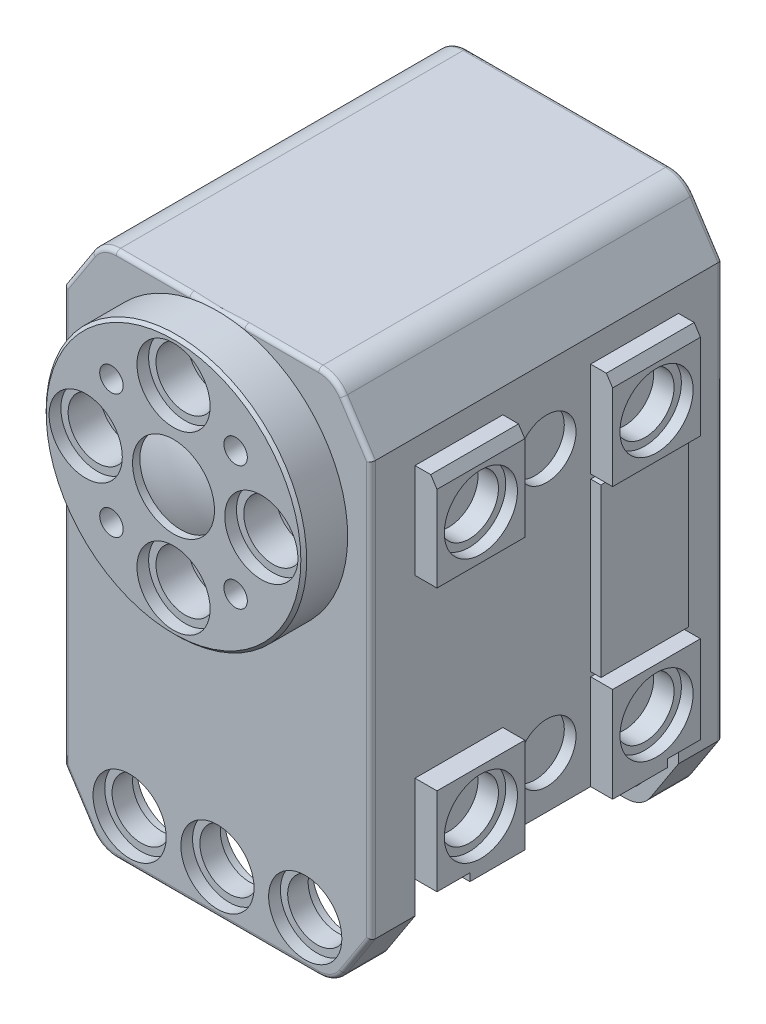
SolidWorks part; units mm, degrees
ref_plane "Front Plane" through (0, 0, 0) normal (0, 0, 1) x (1, 0, 0)
ref_plane "Top Plane" through (0, 0, 0) normal (0, 1, 0) x (1, 0, 0)
ref_plane "Right Plane" through (0, 0, 0) normal (1, 0, 0) x (0, 0, -1)
sketch "Sketch1" plane through (0, 0, 0) normal (0, 1, 0) x (1, 0, 0)
  line L0 (8.9, -12) -> (0, -12)
  line L1 (0, -12) -> (0, -15)
  line L2 (2.8, -14.5) -> (2.8, -15)
  line L3 (2.8, -15) -> (8.9, -15)
  line L4 (8.9, -15) -> (8.9, -12)
  line L5 (0, -12) -> (0, -15) construction
  arc A0 (0, -15) -> (2.8, -14.5) centre (0, -6.91) ccw
revolve "Revolve1" add sketch "Sketch1" angle 360 about L5
ref_plane "Plane1" through (0, 0, 12) normal (0, 0, 1) x (1, 0, 0)
sketch "Sketch2" plane through (0, 0, 12) normal (0, 0, 1) x (1, 0, 0)
  line L0 (12, -23.1503) -> (12, 5.1503)
  line L1 (12, 5.1503) -> (10.5, 5.1503)
  line L2 (10.5, 5.1503) -> (8, 9)
  line L3 (8, 9) -> (-8, 9)
  line L4 (-8, 9) -> (-10.5, 5.1503)
  line L5 (-10.5, 5.1503) -> (-12, 5.1503)
  line L6 (-12, 5.1503) -> (-12, -21.5)
  line L7 (-12, -21.5) -> (-11.5717, -21.5)
  line L8 (-11.5717, -21.5) -> (-8, -27)
  line L9 (-8, -27) -> (8, -27)
  line L10 (8, -27) -> (10.5, -23.1503)
  line L11 (10.5, -23.1503) -> (12, -23.1503)
extrude "Boss-Extrude1" add sketch "Sketch2" against normal blind 3
sketch "Sketch3" plane through (0, -23.1503, 0) normal (0, -1, 0) x (1, 0, 0)
  line L0 (10.5, 9) -> (12, 9)
  line L1 (12, 9) -> (12, 12)
  line L2 (12, 12) -> (10.5, 12)
  line L3 (10.5, 12) -> (10.5, 9)
extrude "Cut-Extrude1" cut sketch "Sketch3" against normal blind 1.6503
sketch "Sketch4" plane through (0, 0, 9) normal (0, 0, -1) x (-1, 0, 0)
  line L0 (-10.5, 5.1503) -> (-8, 9)
  line L1 (-8, 9) -> (8, 9)
  line L2 (8, 9) -> (10.5, 5.1503)
  line L3 (10.5, 5.1503) -> (12, 5.1503)
  line L4 (12, 5.1503) -> (12, -21.5)
  line L5 (12, -21.5) -> (6, -21.5)
  line L6 (4, -22.5) -> (-4, -22.5)
  line L7 (-6, -21.5) -> (-12, -21.5)
  line L8 (-12, -21.5) -> (-12, 5.1503)
  line L9 (-12, 5.1503) -> (-10.5, 5.1503)
  arc A0 (6, -21.5) -> (4, -22.5) centre (6, -24) ccw
  arc A1 (-4, -22.5) -> (-6, -21.5) centre (-6, -24) ccw
extrude "Boss-Extrude2" add sketch "Sketch4" along normal blind 18
sketch "Sketch5" plane through (0, 0, 12) normal (0, 0, 1) x (1, 0, 0)
  line L0 (12, -21.5) -> (12, 5.1503)
  line L1 (12, 5.1503) -> (10.5, 5.1503)
  line L2 (10.5, 5.1503) -> (10.5, -21.5)
  line L3 (10.5, -21.5) -> (12, -21.5)
extrude "Cut-Extrude2" cut sketch "Sketch5" against normal blind 3
sketch "Sketch6" plane through (0, 0, 9) normal (0, 0, -1) x (-1, 0, 0)
  line L0 (10.5, -21.5) -> (10.5, -23.1503)
  line L1 (10.5, -23.1503) -> (11.5717, -21.5)
  line L2 (11.5717, -21.5) -> (10.5, -21.5)
extrude "Cut-Extrude3" cut sketch "Sketch6" against normal through all
sketch "Sketch7" plane through (0, 0, 12) normal (0, 0, 1) x (1, 0, 0)
  line L0 (-10.5, -21.5) -> (-10.5, 5.1503)
  line L1 (-10.5, 5.1503) -> (-12, 5.1503)
  line L2 (-12, 5.1503) -> (-12, -21.5)
  line L3 (-12, -21.5) -> (-10.5, -21.5)
extrude "Cut-Extrude4" cut sketch "Sketch7" against normal blind 3
sketch "Sketch8" plane through (0, 5.1503, 0) normal (0, 1, 0) x (-1, 0, 0)
  line L0 (-12, 9) -> (-12, -9)
  line L1 (-12, -9) -> (-10.5, -9)
  line L2 (-10.5, -9) -> (-10.5, 9)
  line L3 (-10.5, 9) -> (-12, 9)
extrude "Cut-Extrude5" cut sketch "Sketch8" against normal blind 20.1503
sketch "Sketch9" plane through (0, 0, -9) normal (0, 0, -1) x (-1, 0, 0)
  line L0 (-12, -15) -> (-12, -21.5)
  line L1 (-12, -21.5) -> (-10.5, -21.5)
  line L2 (-10.5, -21.5) -> (-10.5, -15)
  line L3 (-10.5, -15) -> (-12, -15)
extrude "Cut-Extrude6" cut sketch "Sketch9" against normal blind 12
sketch "Sketch10" plane through (0, 0, -9) normal (0, 0, -1) x (-1, 0, 0)
  line L0 (-10.5, -20.975) -> (-10.5, -21.5)
  line L1 (-10.5, -21.5) -> (-6, -21.5)
  line L2 (-4, -22.5) -> (-3.3731, -22.5)
  line L3 (-6, -20.975) -> (-10.5, -20.975)
  arc A0 (-6, -21.5) -> (-4, -22.5) centre (-6, -24) cw
  arc A1 (-3.3731, -22.5) -> (-6, -20.975) centre (-6, -24) ccw
extrude "Cut-Extrude7" cut sketch "Sketch10" against normal blind 2.25
sketch "Sketch11" plane through (0, 0, -9) normal (0, 0, -1) x (-1, 0, 0)
  line L0 (3.3731, -22.5) -> (4, -22.5)
  line L1 (6, -21.5) -> (12, -21.5)
  line L2 (12, -21.5) -> (12, -20.975)
  line L3 (12, -20.975) -> (6, -20.975)
  arc A0 (6, -20.975) -> (3.3731, -22.5) centre (6, -24) ccw
  arc A1 (4, -22.5) -> (6, -21.5) centre (6, -24) cw
extrude "Cut-Extrude8" cut sketch "Sketch11" against normal blind 2.25
sketch "Sketch12" plane through (0, 0, 9) normal (0, 0, 1) x (1, 0, 0)
  line L0 (3.3731, -22.5) -> (4, -22.5)
  line L1 (6, -21.5) -> (12, -21.5)
  line L2 (12, -21.5) -> (12, -20.975)
  line L3 (12, -20.975) -> (6, -20.975)
  arc A0 (6, -20.975) -> (3.3731, -22.5) centre (6, -24) ccw
  arc A1 (4, -22.5) -> (6, -21.5) centre (6, -24) cw
extrude "Cut-Extrude9" cut sketch "Sketch12" against normal blind 2.25
sketch "Sketch13" plane through (0, 0, 9) normal (0, 0, 1) x (1, 0, 0)
  line L0 (-6, -20.975) -> (-12, -20.975)
  line L1 (-12, -20.975) -> (-12, -21.5)
  line L2 (-12, -21.5) -> (-6, -21.5)
  line L3 (-4, -22.5) -> (-3.3731, -22.5)
  arc A0 (-3.3731, -22.5) -> (-6, -20.975) centre (-6, -24) ccw
  arc A1 (-6, -21.5) -> (-4, -22.5) centre (-6, -24) cw
extrude "Cut-Extrude10" cut sketch "Sketch13" against normal blind 2.25
sketch "Sketch14" plane through (0, 5.1503, 0) normal (0, 1, 0) x (-1, 0, 0)
  line L0 (10.5, 9) -> (10.5, -3)
  line L1 (10.5, -3) -> (12, -3)
  line L2 (12, -3) -> (12, 9)
  line L3 (12, 9) -> (10.5, 9)
extrude "Cut-Extrude11" cut sketch "Sketch14" against normal blind 20.1503
ref_plane "Plane2" through (0, 0, -3) normal (0, 0, -1) x (-1, 0, 0)
sketch "Sketch15" plane through (0, 0, -3) normal (0, 0, -1) x (-1, 0, 0)
  line L0 (10.5, -15) -> (10.5, -21.5)
  line L1 (10.5, -21.5) -> (12, -21.5)
  line L2 (12, -21.5) -> (12, -15)
  line L3 (12, -15) -> (10.5, -15)
extrude "Cut-Extrude12" cut sketch "Sketch15" against normal blind 6
sketch "Sketch16" plane through (0, 5.1503, 0) normal (0, 1, 0) x (-1, 0, 0)
  line L0 (12, -3) -> (10.5, -3)
  line L1 (10.5, -3) -> (10.5, -9)
  line L2 (10.5, -9) -> (12, -9)
  line L3 (12, -9) -> (12, -3)
extrude "Cut-Extrude13" cut sketch "Sketch16" against normal blind 20.1503
sketch "Sketch17" plane through (10.5, 0, 0) normal (1, 0, 0) x (0, 0, -1)
  line L0 (3, -21.5) -> (3, -15)
  line L1 (3, -15) -> (9, -15)
  line L2 (9, -15) -> (9, -20.975)
  line L3 (9, -20.975) -> (6.75, -20.975)
  line L4 (6.75, -20.975) -> (6.75, -21.5)
  line L5 (6.75, -21.5) -> (3, -21.5)
extrude "Boss-Extrude3" add sketch "Sketch17" along normal blind 1.5
sketch "Sketch18" plane through (0, 0, -9) normal (0, 0, -1) x (-1, 0, 0)
  line L0 (-8, 9) -> (8, 9)
  line L1 (8, 9) -> (10.5, 5.1503)
  line L2 (10.5, 5.1503) -> (10.5, -23.1503)
  line L3 (10.5, -23.1503) -> (8, -27)
  line L4 (8, -27) -> (-8, -27)
  line L5 (-8, -27) -> (-10.5, -23.1503)
  line L6 (-10.5, -23.1503) -> (-10.5, 5.1503)
  line L7 (-10.5, 5.1503) -> (-8, 9)
extrude "Boss-Extrude4" add sketch "Sketch18" along normal blind 3
sketch "Sketch19" plane through (0, 0, 9) normal (0, 0, -1) x (-1, 0, 0)
  circle A0 centre (6, -24) radius 2.5
extrude "Cut-Extrude14" cut sketch "Sketch19" against normal blind 0.8
sketch "Sketch20" plane through (0, 0, 12) normal (0, 0, 1) x (1, 0, 0)
  circle A0 centre (-6, -24) radius 2.5
extrude "Cut-Extrude15" cut sketch "Sketch20" against normal blind 0.8
sketch "Sketch21" plane through (0, 0, 11.2) normal (0, 0, 1) x (1, 0, 0)
  circle A0 centre (-6, -24) radius 2
extrude "Cut-Extrude16" cut sketch "Sketch21" against normal up to next
sketch "Sketch22" plane through (0, 0, -9) normal (0, 0, 1) x (1, 0, 0)
  circle A0 centre (-6, -24) radius 2.5
extrude "Cut-Extrude17" cut sketch "Sketch22" against normal blind 0.8
sketch "Sketch23" plane through (0, 0, -12) normal (0, 0, -1) x (-1, 0, 0)
  circle A0 centre (6, -24) radius 2.5
extrude "Cut-Extrude18" cut sketch "Sketch23" against normal blind 0.8
sketch "Sketch24" plane through (0, 0, -11.2) normal (0, 0, -1) x (-1, 0, 0)
  circle A0 centre (6, -24) radius 2
extrude "Cut-Extrude19" cut sketch "Sketch24" against normal up to next
sketch "Sketch25" plane through (-10.5, 0, 0) normal (-1, 0, 0) x (0, 0, 1)
  line L0 (3, 3.5) -> (9, 3.5)
  line L1 (9, 3.5) -> (9, -3)
  line L2 (9, -3) -> (3, -3)
  line L3 (3, -3) -> (3, 3.5)
extrude "Boss-Extrude5" add sketch "Sketch25" along normal blind 1.5
sketch "Sketch26" plane through (-10.5, 0, 0) normal (-1, 0, 0) x (0, 0, 1)
  line L0 (-3, -3) -> (-9, -3)
  line L1 (-9, -3) -> (-9, 3.5)
  line L2 (-9, 3.5) -> (-3, 3.5)
  line L3 (-3, 3.5) -> (-3, -3)
extrude "Boss-Extrude6" add sketch "Sketch26" along normal blind 1.5
sketch "Sketch27" plane through (10.5, 0, 0) normal (1, 0, 0) x (0, 0, -1)
  line L0 (-3, -3) -> (-9, -3)
  line L1 (-9, -3) -> (-9, 3.5)
  line L2 (-9, 3.5) -> (-3, 3.5)
  line L3 (-3, 3.5) -> (-3, -3)
extrude "Boss-Extrude7" add sketch "Sketch27" along normal blind 1.5
sketch "Sketch28" plane through (10.5, 0, 0) normal (1, 0, 0) x (0, 0, -1)
  line L0 (3, 3.5) -> (9, 3.5)
  line L1 (9, 3.5) -> (9, -3)
  line L2 (9, -3) -> (3, -3)
  line L3 (3, -3) -> (3, 3.5)
extrude "Boss-Extrude8" add sketch "Sketch28" along normal blind 1.5
sketch "Sketch29" plane through (10.5, 0, 0) normal (1, 0, 0) x (0, 0, -1)
  line L0 (3, -3.3) -> (9, -3.3)
  line L1 (9, -3.3) -> (9, -14.7)
  line L2 (9, -14.7) -> (3, -14.7)
  line L3 (3, -14.7) -> (3, -3.3)
extrude "Boss-Extrude9" add sketch "Sketch29" along normal blind 0.7
sketch "Sketch30" plane through (-10.5, 0, 0) normal (-1, 0, 0) x (0, 0, 1)
  line L0 (-3, -14.7) -> (-9, -14.7)
  line L1 (-9, -14.7) -> (-9, -3.3)
  line L2 (-9, -3.3) -> (-3, -3.3)
  line L3 (-3, -3.3) -> (-3, -14.7)
extrude "Boss-Extrude10" add sketch "Sketch30" along normal blind 0.7
ref_plane "Plane3" through (0, -24, 0) normal (0, 1, 0) x (1, 0, 0)
sketch "Sketch31" plane through (0, -24, 0) normal (0, 1, 0) x (1, 0, 0)
  line L0 (2.5, -9) -> (0, -9)
  line L1 (0, -9) -> (0, -12)
  line L2 (0, -12) -> (2.5, -12)
  line L3 (2.5, -12) -> (2.5, -11.2)
  line L4 (2.5, -11.2) -> (2, -11.2)
  line L5 (2, -11.2) -> (2, -9.8)
  line L6 (2, -9.8) -> (2.5, -9.8)
  line L7 (2.5, -9.8) -> (2.5, -9)
  line L8 (0, -9) -> (0, -12) construction
revolve "Cut-Revolve1" cut sketch "Sketch31" angle 360 about L8
sketch "Sketch32" plane through (0, -24, 0) normal (0, 1, 0) x (1, 0, 0)
  line L0 (2.5, 12) -> (0, 12)
  line L1 (0, 12) -> (0, 9)
  line L2 (0, 9) -> (2.5, 9)
  line L3 (2.5, 9) -> (2.5, 9.8)
  line L4 (2.5, 9.8) -> (2, 9.8)
  line L5 (2, 9.8) -> (2, 11.2)
  line L6 (2, 11.2) -> (2.5, 11.2)
  line L7 (2.5, 11.2) -> (2.5, 12)
  line L8 (0, 12) -> (0, 9) construction
revolve "Cut-Revolve2" cut sketch "Sketch32" angle 360 about L8
sketch "Sketch33" plane through (0, -24, 0) normal (0, 1, 0) x (1, 0, 0)
  line L0 (8.5, 12) -> (6, 12)
  line L1 (6, 12) -> (6, 9)
  line L2 (6, 9) -> (8.5, 9)
  line L3 (8.5, 9) -> (8.5, 9.8)
  line L4 (8.5, 9.8) -> (8, 9.8)
  line L5 (8, 9.8) -> (8, 11.2)
  line L6 (8, 11.2) -> (8.5, 11.2)
  line L7 (8.5, 11.2) -> (8.5, 12)
  line L8 (6, 12) -> (6, 9) construction
revolve "Cut-Revolve3" cut sketch "Sketch33" angle 360 about L8
sketch "Sketch34" plane through (0, -24, 0) normal (0, 1, 0) x (1, 0, 0)
  line L0 (8.5, -9) -> (6, -9)
  line L1 (6, -9) -> (6, -12)
  line L2 (6, -12) -> (8.5, -12)
  line L3 (8.5, -12) -> (8.5, -11.2)
  line L4 (8.5, -11.2) -> (8, -11.2)
  line L5 (8, -11.2) -> (8, -9.8)
  line L6 (8, -9.8) -> (8.5, -9.8)
  line L7 (8.5, -9.8) -> (8.5, -9)
  line L8 (6, -9) -> (6, -12) construction
revolve "Cut-Revolve4" cut sketch "Sketch34" angle 360 about L8
hole_wizard "Ø4.0 (4) Diameter Hole1" positions "Sketch36" profile "Sketch35" hole size "Ø4.0" standard "ANSI Metric"
sketch "Sketch36" plane through (-10.5, 0, 0) normal (-1, 0, 0) x (0, 0, 1)
  point P0 (0, 0)
  point P1 (0, -18)
sketch "Sketch35" plane through (-10.5, 0, 0) normal (0, 1, 0) x (0, 0, 1)
  line L0 (0, 0) -> (0, 0.8)
  line L1 (0, 0.8) -> (2, 0.8)
  line L2 (2, 0.8) -> (2, 0)
  line L5 (2, 0) -> (0, 0)
  line L10 (0, 0.8) -> (-2, 0.8) construction
  line L11 (0, -6.35) -> (0, 107.95) construction
  dimension "Hole Dia." = 4
  dimension "Hole Depth" = 0.8
  dimension "Drill Angle" = 180
hole_wizard "Ø4.0 (4) Diameter Hole2" positions "Sketch38" profile "Sketch37" hole size "Ø4.0" standard "ANSI Metric"
sketch "Sketch38" plane through (10.5, 0, 0) normal (1, 0, 0) x (0, 0, -1)
  point P0 (0, 0)
  point P1 (0, -18)
sketch "Sketch37" plane through (10.5, 0, 0) normal (0, 1, 0) x (0, 0, -1)
  line L0 (0, 0) -> (0, 0.8)
  line L1 (0, 0.8) -> (2, 0.8)
  line L2 (2, 0.8) -> (2, 0)
  line L5 (2, 0) -> (0, 0)
  line L10 (0, 0.8) -> (-2, 0.8) construction
  line L11 (0, -6.35) -> (0, 107.95) construction
  dimension "Hole Dia." = 4
  dimension "Hole Depth" = 0.8
  dimension "Drill Angle" = 180
hole_wizard "CBORE for M3.5 Hex Head Machine Screw1" positions "Sketch40" profile "Sketch39" counterbore size "M3.5" standard "ANSI Metric"
sketch "Sketch40" plane through (12, 0, 0) normal (1, 0, 0) x (0, 0, -1)
  point P0 (6, 0)
  point P1 (-6, 0)
  point P2 (6, -18)
  point P3 (-6, -18)
sketch "Sketch39" plane through (12, 0, -6) normal (0, 1, 0) x (0, 0, -1)
  line L0 (0, 0) -> (0, 2.2)
  line L1 (0, 2.2) -> (2, 2.2)
  line L2 (2, 2.2) -> (2, 0.8)
  line L3 (2, 0.8) -> (2.5, 0.8)
  line L4 (2.5, 0.8) -> (2.5, 0)
  line L5 (2.5, 0) -> (0, 0)
  line L10 (0, 2.2) -> (-2, 2.2) construction
  line L11 (0, -6.35) -> (0, 107.95) construction
  dimension "Hole Dia." = 4
  dimension "Hole Depth" = 2.2
  dimension "C'Bore Dia." = 5
  dimension "C'Bore Depth" = 0.8
  dimension "Drill Angle" = 180
hole_wizard "CBORE for M3.5 Hex Head Machine Screw2" positions "Sketch42" profile "Sketch41" counterbore size "M3.5" standard "ANSI Metric"
sketch "Sketch42" plane through (-12, 0, 0) normal (-1, 0, 0) x (0, 0, 1)
  point P0 (-6, 0)
  point P1 (6, 0)
  point P2 (-6, -18)
  point P3 (6, -18)
sketch "Sketch41" plane through (-12, 0, -6) normal (0, 1, 0) x (0, 0, 1)
  line L0 (0, 0) -> (0, 2.2)
  line L1 (0, 2.2) -> (2, 2.2)
  line L2 (2, 2.2) -> (2, 0.8)
  line L3 (2, 0.8) -> (2.5, 0.8)
  line L4 (2.5, 0.8) -> (2.5, 0)
  line L5 (2.5, 0) -> (0, 0)
  line L10 (0, 2.2) -> (-2, 2.2) construction
  line L11 (0, -6.35) -> (0, 107.95) construction
  dimension "Hole Dia." = 4
  dimension "Hole Depth" = 2.2
  dimension "C'Bore Dia." = 5
  dimension "C'Bore Depth" = 0.8
  dimension "Drill Angle" = 180
hole_wizard "CBORE for M3.5 Hex Head Machine Screw3" positions "Sketch44" profile "Sketch43" counterbore size "M3.5" standard "ANSI Metric"
sketch "Sketch44" plane through (0, 0, -12) normal (0, 0, -1) x (-1, 0, 0)
  point P0 (6, 0)
  point P1 (0, 0)
  point P2 (-6, 0)
sketch "Sketch43" plane through (-6, 0, -12) normal (1, 0, 0) x (0, 1, 0)
  line L0 (0, 0) -> (0, 3)
  line L1 (0, 3) -> (2, 3)
  line L2 (2, 3) -> (2, 0.8)
  line L3 (2, 0.8) -> (2.5, 0.8)
  line L4 (2.5, 0.8) -> (2.5, 0)
  line L5 (2.5, 0) -> (0, 0)
  line L10 (0, 3) -> (-2, 3) construction
  line L11 (0, -6.35) -> (0, 107.95) construction
  dimension "Hole Dia." = 4
  dimension "Hole Depth" = 3
  dimension "C'Bore Dia." = 5
  dimension "C'Bore Depth" = 0.8
  dimension "Drill Angle" = 180
hole_wizard "Ø1.6 (1.6) Diameter Hole1" positions "Sketch46" profile "Sketch45" hole size "Ø1.6" standard "ANSI Metric"
sketch "Sketch46" plane through (0, 0, 15) normal (0, 0, 1) x (1, 0, 0)
  point P0 (4.2426, 4.2426)
  point P1 (-4.2426, 4.2426)
  point P2 (4.2426, -4.2426)
  point P3 (-4.2426, -4.2426)
sketch "Sketch45" plane through (4.2426, 4.2426, 15) normal (1, 0, 0) x (0, -1, 0)
  line L0 (0, 0) -> (0, 3)
  line L1 (0, 3) -> (0.8, 3)
  line L2 (0.8, 3) -> (0.8, 0)
  line L5 (0.8, 0) -> (0, 0)
  line L10 (0, 3) -> (-0.8, 3) construction
  line L11 (0, -6.35) -> (0, 107.95) construction
  dimension "Hole Dia." = 1.6
  dimension "Hole Depth" = 3
  dimension "Drill Angle" = 180
hole_wizard "CBORE for M3.5 Hex Head Machine Screw4" positions "Sketch48" profile "Sketch47" counterbore size "M3.5" standard "ANSI Metric"
sketch "Sketch48" plane through (0, 0, 15) normal (0, 0, 1) x (1, 0, 0)
  point P0 (6, 0)
  point P1 (0, 6)
  point P2 (-6, 0)
  point P3 (0, -6)
sketch "Sketch47" plane through (6, 0, 15) normal (1, 0, 0) x (0, -1, 0)
  line L0 (0, 0) -> (0, 3)
  line L1 (0, 3) -> (2, 3)
  line L2 (2, 3) -> (2, 0.8)
  line L3 (2, 0.8) -> (2.5, 0.8)
  line L4 (2.5, 0.8) -> (2.5, 0)
  line L5 (2.5, 0) -> (0, 0)
  line L10 (0, 3) -> (-2, 3) construction
  line L11 (0, -6.35) -> (0, 107.95) construction
  dimension "Hole Dia." = 4
  dimension "Hole Depth" = 3
  dimension "C'Bore Dia." = 5
  dimension "C'Bore Depth" = 0.8
  dimension "Drill Angle" = 180
fillet "Fillet1" radius 2 6 edges at (-8, -27, -10.5) (8, -27, 10.5) (8, 9, 0) (-8, 9, 0) (8, -27, -10.5) (-8, -27, 10.5)
chamfer "Chamfer2" distance 0.4283 angle 57 4 edges at (-12, 3.5, -6) (-12, 3.5, 6) (12, 3.5, -6) (12, 3.5, 6)
chamfer "Chamfer4" distance 0.2 angle 45 1 edges at (8.9, 0, 15)
fillet "Fillet2" radius 0.3 24 edges at (-9.5457, -24.6198, 12) (-7.8684, -26.7576, 12) (0, -27, 12) (7.8684, -26.7576, 12) (9.5457, -24.6198, 12) (-10.5, -9, 12) (10.5, -9, 12) (-9.5457, 6.6198, 12) (9.5457, 6.6198, 12) (-7.8684, 8.7576, 12) (7.8684, 8.7576, 12) (0, 9, 12) (-9.5457, -24.6198, -12) (9.5457, -24.6198, -12) (-7.8684, -26.7576, -12) (7.8684, -26.7576, -12) (0, -27, -12) (10.5, -9, -12) (-10.5, -9, -12) (9.5457, 6.6198, -12) (-9.5457, 6.6198, -12) (7.8684, 8.7576, -12) (-7.8684, 8.7576, -12) (0, 9, -12)
